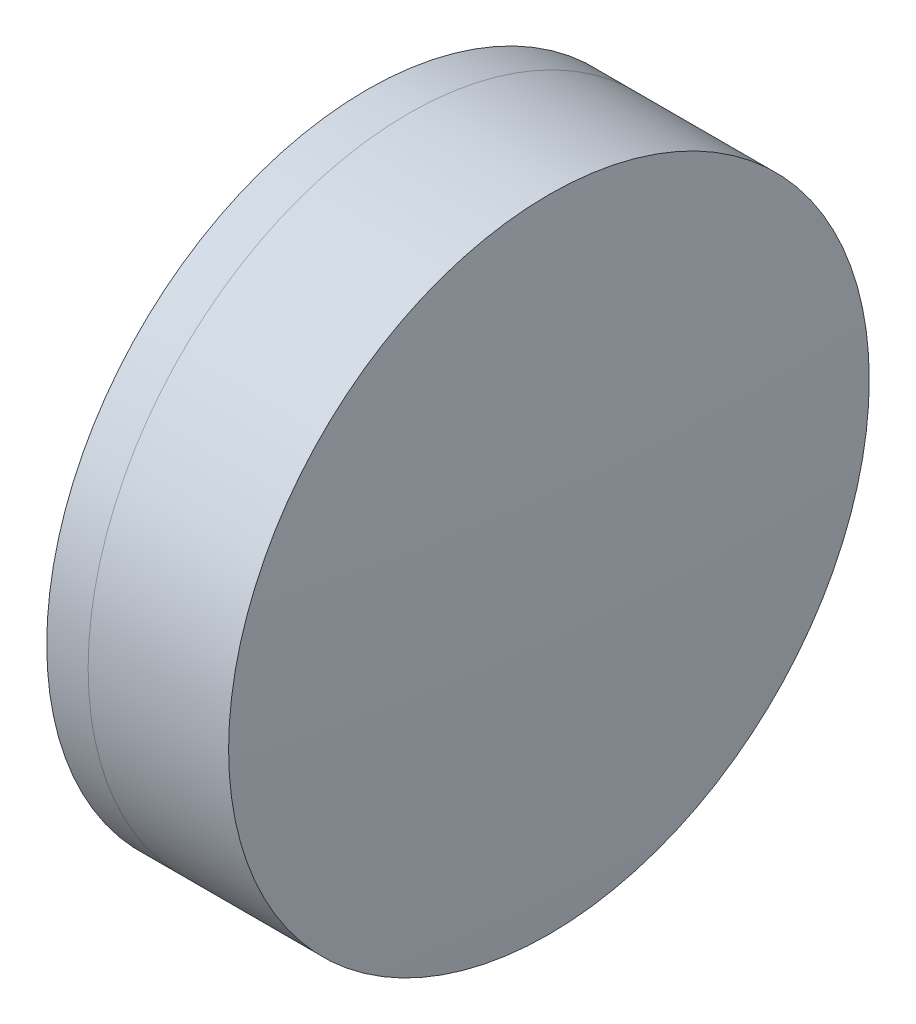
SolidWorks part; units mm, degrees
ref_plane "前视基准面" through (0, 0, 0) normal (0, 0, 1) x (1, 0, 0)
ref_plane "上视基准面" through (0, 0, 0) normal (0, 1, 0) x (1, 0, 0)
ref_plane "右视基准面" through (0, 0, 0) normal (1, 0, 0) x (0, 0, -1)
sketch "草图1" plane through (0, 0, 0) normal (0, 1, 0) x (1, 0, 0)
  line L0 (124.5233, 0) -> (395.1269, 0) construction
  line L1 (302.3027, -25.4) -> (305.5838, -25.4)
  line L2 (302.3027, 25.4) -> (305.5838, 25.4)
  arc A0 (305.5838, -25.4) -> (305.5838, 25.4) centre (269.4109, 0) ccw
  arc A1 (302.3027, 25.4) -> (302.3027, -25.4) centre (368.7109, 0) ccw
  point P10 (297.6109, 0)
  point P11 (313.6109, 0)
  dimension "D3" = 71.1
  dimension "D4" = 44.2
  dimension "D1" = 25.4
  dimension "D2" = 25.4
  dimension "D5" = 16
revolve "旋转1" add sketch "草图1" angle 360 about L0
sketch "草图2" plane through (0, 0, 0) normal (0, 1, 0) x (1, 0, 0)
  line L0 (-0.5519, 0) -> (409.4962, 0) construction
  line L2 (305.5838, 25.4) -> (316.7214, 25.4)
  line L3 (305.5838, -25.4) -> (316.7214, -25.4)
  arc A0 (316.7214, -25.4) -> (316.7214, 25.4) centre (-45.4891, 0) ccw
  arc A1 (305.5838, -25.4) -> (305.5838, 25.4) centre (269.4109, 0) ccw construction
  arc A2 (305.5838, -25.4) -> (305.5838, 25.4) centre (269.4109, 0) ccw
  point P4 (313.6109, 0)
  point P8 (317.6109, 0)
  dimension "D1" = 363.1
  dimension "D2" = 4
revolve "旋转3" add sketch "草图2" angle 360 about L0
